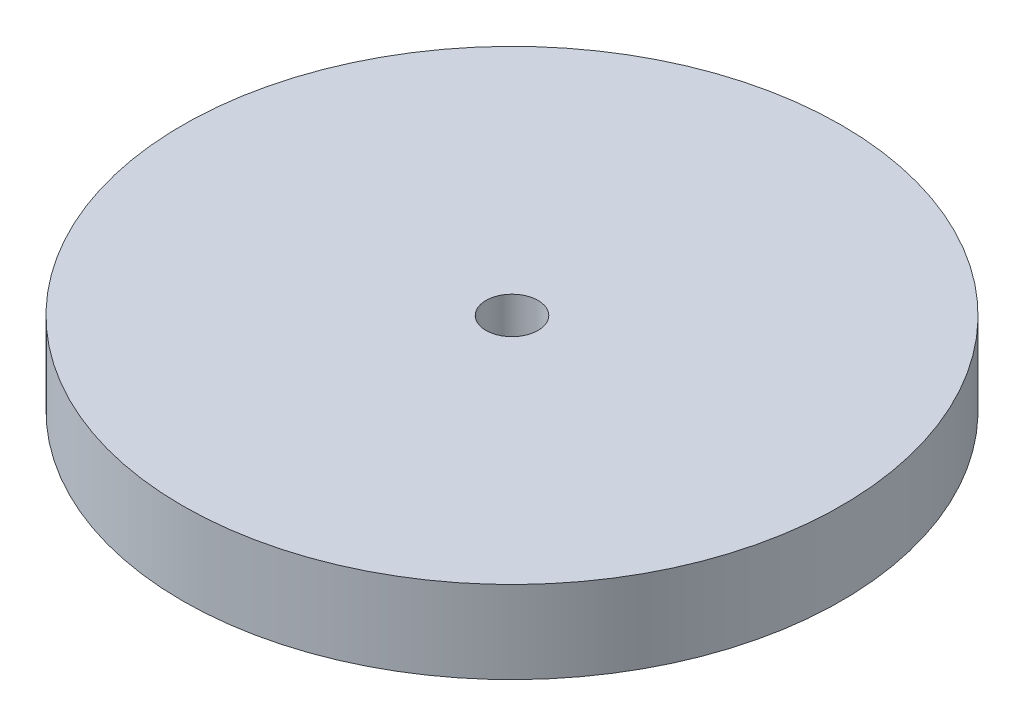
SolidWorks part; units mm, degrees
ref_plane "Front" through (0, 0, 0) normal (0, 0, 1) x (1, 0, 0)
ref_plane "Top" through (0, 0, 0) normal (0, 1, 0) x (1, 0, 0)
ref_plane "Right" through (0, 0, 0) normal (1, 0, 0) x (0, 0, -1)
sketch "Sketch1" plane through (0, 0, 0) normal (0, 1, 0) x (1, 0, 0)
  circle A0 centre (0, 0) radius 25.4
  circle A1 centre (0, 0) radius 2.0066
  dimension "D1" = 50.8
  dimension "D2" = 4.0132
extrude "Boss-Extrude1" add sketch "Sketch1" along normal blind 6.35
